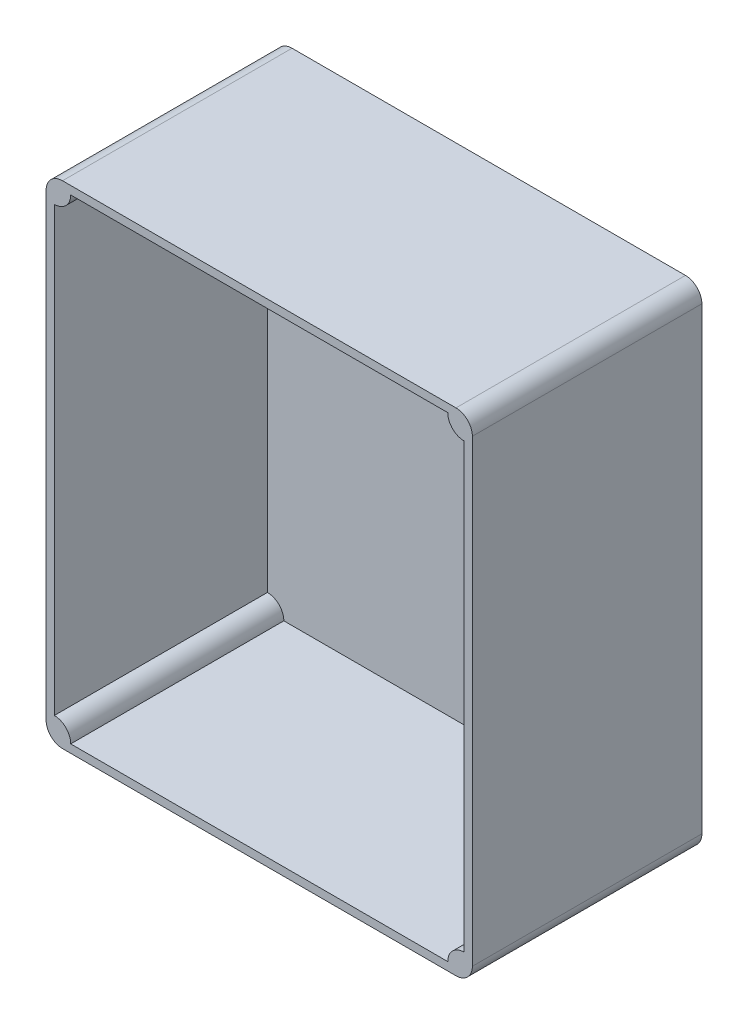
SolidWorks part; units mm, degrees
ref_plane "Front Plane" through (0, 0, 0) normal (0, 0, 1) x (1, 0, 0)
ref_plane "Top Plane" through (0, 0, 0) normal (0, 1, 0) x (1, 0, 0)
ref_plane "Right Plane" through (0, 0, 0) normal (1, 0, 0) x (0, 0, -1)
sketch "Sketch2" plane through (0, 0, 0) normal (0, 0, 1) x (1, 0, 0)
  line L1 (-65, 75) -> (65, 75)
  line L2 (-65, 75) -> (-65, -75)
  line L3 (-65, -75) -> (65, -75)
  line L4 (65, 75) -> (65, -75)
  line L5 (-65, 75) -> (65, -75) construction
  line L6 (-65, -75) -> (65, 75) construction
  point P0 (0, 0)
  dimension "D1" = 130
  dimension "D2" = 150
extrude "Boss-Extrude2" add sketch "Sketch2" along normal mid plane 70
sketch "Sketch3" plane through (0, 0, 35) normal (0, 0, 1) x (1, 0, 0)
  line L1 (-62.5, 72.5) -> (62.5, 72.5)
  line L2 (-62.5, 72.5) -> (-62.5, -72.5)
  line L3 (-62.5, -72.5) -> (62.5, -72.5)
  line L4 (62.5, 72.5) -> (62.5, -72.5)
  line L5 (-62.5, 72.5) -> (62.5, -72.5) construction
  line L6 (-62.5, -72.5) -> (62.5, 72.5) construction
  arc A0 (62.5, -67.5) -> (57.5, -72.5) centre (62.5, -72.5) ccw
  arc A1 (-57.5, -72.5) -> (-62.5, -67.5) centre (-62.5, -72.5) ccw
  arc A2 (-57.5, 72.5) -> (-62.5, 67.5) centre (-62.5, 72.5) cw
  arc A3 (57.5, 72.5) -> (62.5, 67.5) centre (62.5, 72.5) ccw
  point P0 (0, 0)
  dimension "D3" = 5
  dimension "D4" = 5
  dimension "D5" = 5
  dimension "D6" = 5
  dimension "D1" = 125
  dimension "D2" = 145
extrude "Cut-Extrude2" cut sketch "Sketch3" against normal blind 65 contours A3 L1 A2 L2 A1 L3 A0 L4
fillet "Fillet1" radius 5 4 edges at (-65, 75, 0) (65, 75, 0) (65, -75, 0) (-65, -75, 0)
